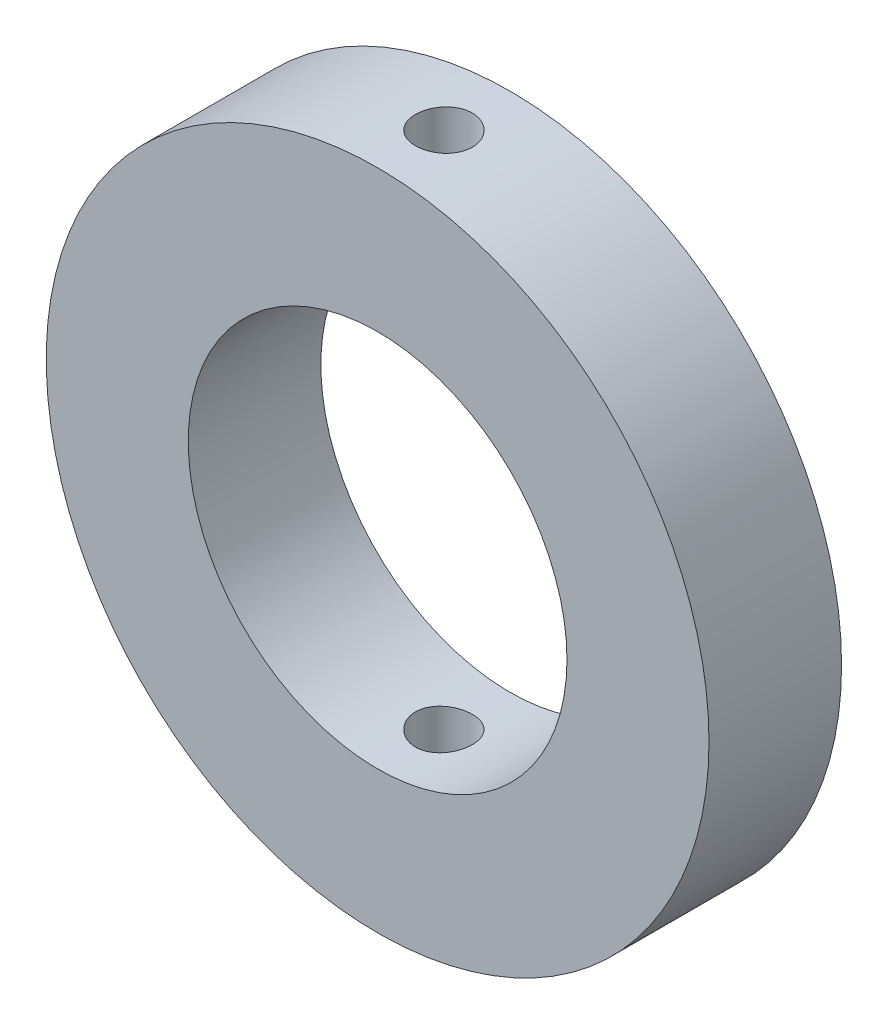
SolidWorks part; units mm, degrees
material "6061-O (SS)"
ref_plane "Front Plane" through (0, 0, 0) normal (0, 0, 1) x (1, 0, 0)
ref_plane "Top Plane" through (0, 0, 0) normal (0, 1, 0) x (1, 0, 0)
ref_plane "Right Plane" through (0, 0, 0) normal (1, 0, 0) x (0, 0, -1)
sketch "Sketch2" plane through (0, 0, 0) normal (0, 0, 1) x (1, 0, 0)
  circle A0 centre (0, 0) radius 17.5
  circle A1 centre (0, 0) radius 10
  dimension "D1" = 20
  dimension "D2" = 35
extrude "Boss-Extrude1" add sketch "Sketch2" along normal blind 7
sketch "Sketch3" plane through (0, 0, 0) normal (0, 1, 0) x (1, 0, 0)
  circle A0 centre (0, -3.5) radius 1.5
extrude "Cut-Extrude1" cut sketch "Sketch3" against normal through all both and the other way through all contours A0
